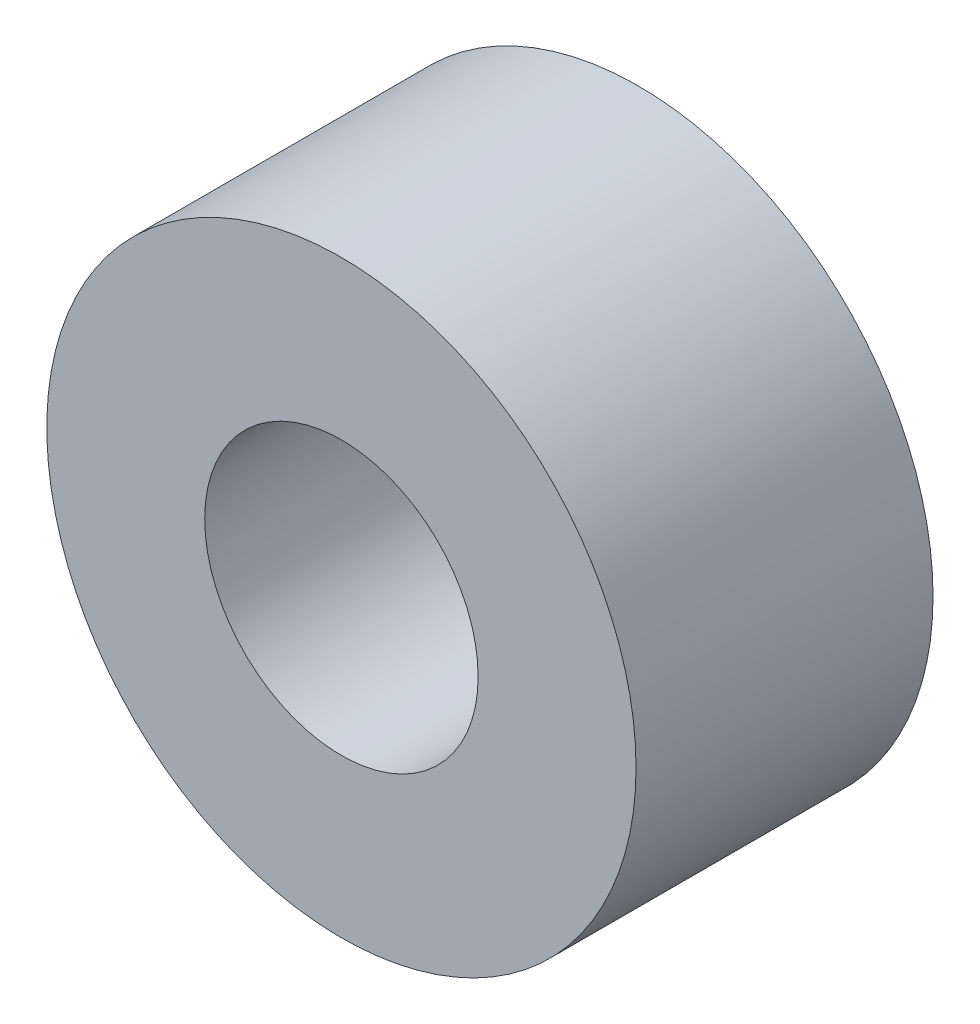
SolidWorks part; units mm, degrees
ref_plane "Front Plane" through (0, 0, 0) normal (0, 0, 1) x (1, 0, 0)
ref_plane "Top Plane" through (0, 0, 0) normal (0, 1, 0) x (1, 0, 0)
ref_plane "Right Plane" through (0, 0, 0) normal (1, 0, 0) x (0, 0, -1)
sketch "Sketch1" plane through (0, 0, 0) normal (0, 0, 1) x (1, 0, 0)
  circle A0 centre (0, 0) radius 3.175
  circle A1 centre (0, 0) radius 1.4732
  dimension "D1" = 2.9464
  dimension "D2" = 6.35
extrude "Boss-Extrude1" add sketch "Sketch1" along normal blind 3.2004
